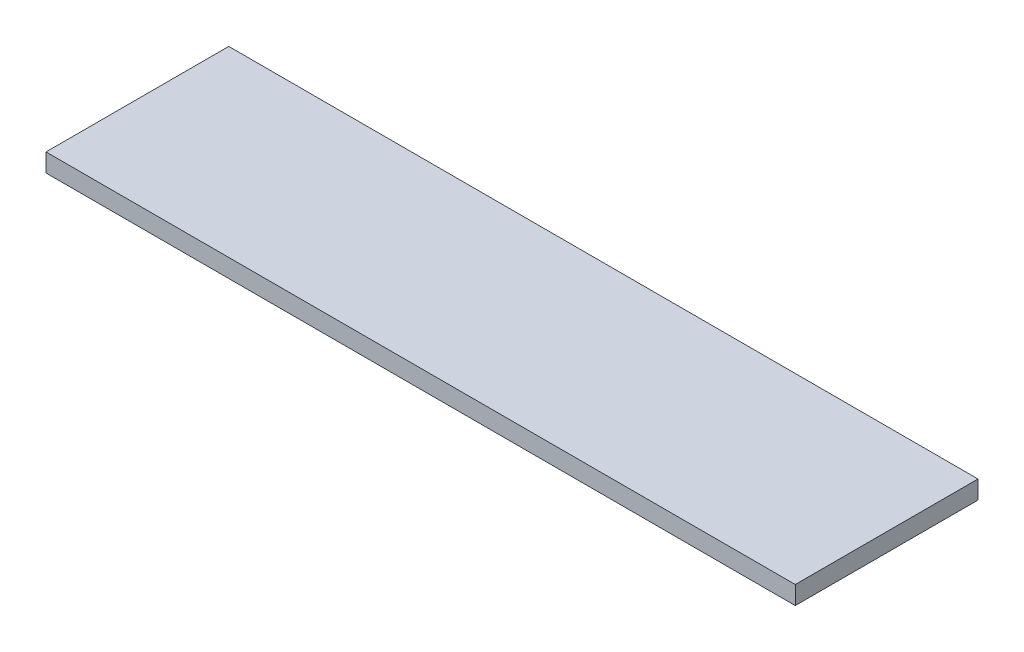
SolidWorks part; units mm, degrees
ref_plane "Front Plane" through (0, 0, 0) normal (0, 0, 1) x (1, 0, 0)
ref_plane "Top Plane" through (0, 0, 0) normal (0, 1, 0) x (1, 0, 0)
ref_plane "Right Plane" through (0, 0, 0) normal (1, 0, 0) x (0, 0, -1)
sketch "Sketch1" plane through (0, 0, 0) normal (0, 1, 0) x (1, 0, 0)
  line L0 (-205, 50) -> (205, -50) construction
  line L1 (-205, 50) -> (205, 50)
  line L2 (-205, 50) -> (-205, -50)
  line L3 (-205, -50) -> (205, -50)
  line L4 (205, 50) -> (205, -50)
  dimension "D1" = 410
  dimension "D2" = 100
extrude "Boss-Extrude1" add sketch "Sketch1" along normal blind 10
